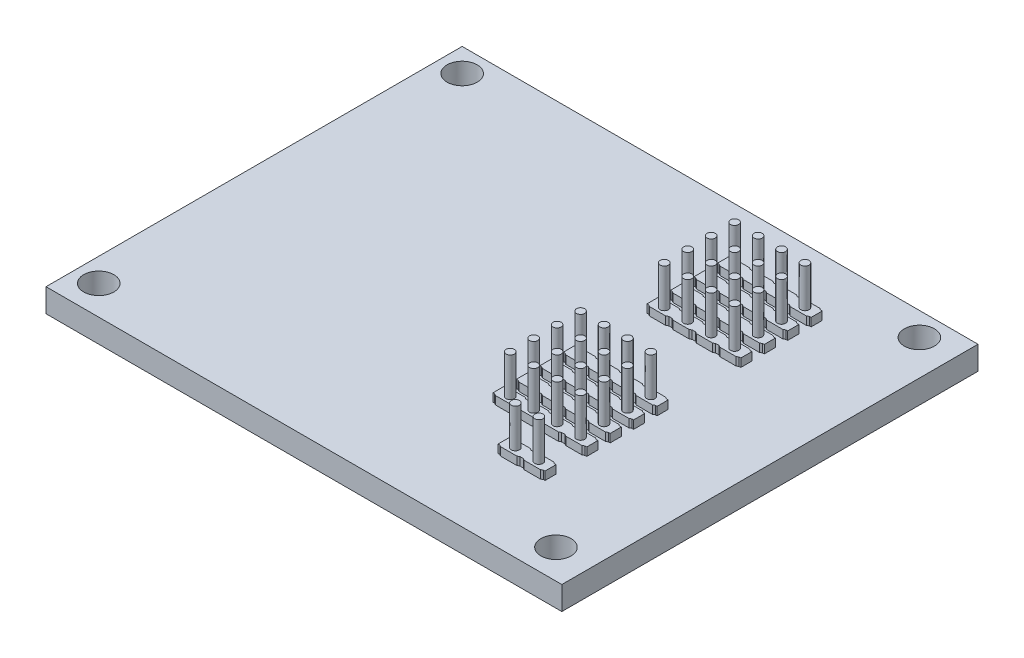
SolidWorks part; units mm, degrees
material "6061-T6 (SS)"
ref_plane "Front Plane" through (0, 0, 0) normal (0, 0, 1) x (1, 0, 0)
ref_plane "Top Plane" through (0, 0, 0) normal (0, 1, 0) x (1, 0, 0)
ref_plane "Right Plane" through (0, 0, 0) normal (1, 0, 0) x (0, 0, -1)
sketch "Sketch1" plane through (0, 0, 0) normal (0, 1, 0) x (1, 0, 0)
  line L1 (-27.94, -22.5425) -> (27.94, -22.5425)
  line L2 (-27.94, -22.5425) -> (-27.94, 22.5425)
  line L3 (-27.94, 22.5425) -> (27.94, 22.5425)
  line L4 (27.94, -22.5425) -> (27.94, 22.5425)
  line L5 (-27.94, -22.5425) -> (27.94, 22.5425) construction
  line L6 (-27.94, 22.5425) -> (27.94, -22.5425) construction
  point P0 (0, 0)
  dimension "D1" = 55.88
  dimension "D2" = 45.085
extrude "Boss-Extrude1" add sketch "Sketch1" along normal blind 2.54
hole_wizard "#4 Clearance Hole1" positions "Sketch2" profile "Sketch3" hole size "#4" standard "ANSI Inch" end condition up to next
sketch "Sketch2" plane through (0, 2.54, 0) normal (0, 1, 0) x (1, 0, 0)
  line L0 (27.94, 22.5425) -> (-27.94, 22.5425) construction
  line L1 (-27.94, 22.5425) -> (-27.94, -22.5425) construction
  point P0 (-25.4, -19.3675)
  point P2 (-25.4, 20.0025)
  point P4 (24.13, 20.0025)
  point P6 (24.13, -19.3675)
  dimension "D1" = 2.54
  dimension "D2" = 2.54
  dimension "D3" = 49.53
  dimension "D4" = 39.37
sketch "Sketch3" plane through (-25.4, 2.54, 19.3675) normal (1, 0, 0) x (0, 0, 1)
  line L0 (0, 0) -> (0, 2.54)
  line L1 (0, 2.54) -> (1.6319, 2.54)
  line L2 (1.6319, 2.54) -> (1.6319, 0)
  line L5 (1.6319, 0) -> (0, 0)
  line L11 (0, -6.35) -> (0, 107.95) construction
  dimension "Thru Hole Dia." = 3.2639
  dimension "Thru Hole Depth" = 2.54
sketch "Sketch4" plane through (0, 2.54, 0) normal (0, 1, 0) x (1, 0, 0)
  line L0 (27.94, 22.5425) -> (-27.94, 22.5425) construction
  line L1 (-27.94, 22.5425) -> (-27.94, -22.5425) construction
  circle A0 centre (16.002, 15.7353) radius 0.4445
  circle A1 centre (16.002, -0.9525) radius 0.4445
  dimension "D1" = 0.889
  dimension "D2" = 6.8072
  dimension "D3" = 43.942
  dimension "D4" = 23.495
extrude "Cut-Extrude1" cut sketch "Sketch4" against normal through all
pattern_linear "LPattern1" count 4 spacing 2.54 along (0, 0, 1) count 4 spacing 2.54 along (-1, 0, 0) of "Cut-Extrude1"
sketch "Sketch5" plane through (0, 2.54, 0) normal (0, 1, 0) x (1, 0, 0)
  circle A0 centre (16.002, -13.0845) radius 0.4445
  circle A1 centre (13.462, -13.0845) radius 0.4445
  circle A2 centre (16.002, -8.5725) radius 0.4445 construction
  point P6 (16.002, -8.5725)
  point P7 (13.462, -8.5725)
extrude "Cut-Extrude2" cut sketch "Sketch5" against normal through all
sketch "Sketch6" plane through (0, 2.54, 0) normal (0, 1, 0) x (1, 0, 0)
  line L0 (15.1229, 16.458) -> (14.918, 16.3342)
  line L1 (15.1229, 16.458) -> (16.8811, 16.458)
  line L2 (15.1229, 16.458) -> (15.1229, 15.0126)
  line L3 (15.1229, 15.0126) -> (16.8811, 15.0126)
  line L4 (16.8811, 16.458) -> (16.8811, 15.0126)
  line L5 (15.1229, 16.458) -> (16.8811, 15.0126) construction
  line L6 (15.1229, 15.0126) -> (16.8811, 16.458) construction
  line L7 (14.918, 16.3342) -> (14.732, 16.3342)
  line L8 (14.732, 16.3342) -> (14.732, 15.1364)
  line L9 (14.732, 15.1364) -> (14.918, 15.1364)
  line L10 (14.918, 15.1364) -> (15.1229, 15.0126)
  line L11 (16.002, 15.7353) -> (14.732, 15.7353) construction
  line L12 (16.002, 15.7353) -> (16.002, 15.0126) construction
  line L13 (16.8811, 16.458) -> (17.086, 16.3342)
  line L14 (16.002, 15.7353) -> (13.462, 15.7353) construction
  line L15 (14.732, 15.7353) -> (14.732, 15.1784) construction
  line L16 (17.086, 15.1364) -> (16.8811, 15.0126)
  line L17 (17.272, 15.7353) -> (17.272, 15.1784) construction
  line L18 (17.272, 15.1364) -> (17.086, 15.1364)
  line L19 (17.272, 16.3342) -> (17.272, 15.1364)
  line L20 (17.086, 16.3342) -> (17.272, 16.3342)
  point P0 (16.002, 15.7353)
  circle M18 centre (16.002, 15.7353) radius 0.4445
extrude "Boss-Extrude2" add sketch "Sketch6" along normal blind 0.889 contours L20 L13 L4 L16 L18 L19 | L4 L1 L2 L3 M18 | L9 L10 L2 L0 L7 L8
pattern_linear "LPattern3" count 4 spacing 2.54 along (0, 0, 1) count 4 spacing 2.54 along (-1, 0, 0) of "Boss-Extrude2"
pattern_linear "LPattern4" count 2 spacing 16.6878 along (0, 0, 1) of "Boss-Extrude2"
pattern_linear "LPattern5" count 4 spacing 2.54 along (0, 0, 1) count 4 spacing 2.54 along (-1, 0, 0) of "LPattern4"
pattern_linear "LPattern6" count 2 spacing 28.829 along (0, 0, 1) of "Boss-Extrude2"
pattern_linear "LPattern7" count 2 spacing 2.54 along (-1, 0, 0) of "LPattern6"
sketch "Sketch7" plane through (0, 2.54, 0) normal (0, 1, 0) x (1, 0, 0)
  circle A0 centre (16.002, 15.7353) radius 0.4445
  circle A1 centre (16.002, 15.7353) radius 0.4445 construction
  circle A2 centre (13.462, 15.7353) radius 0.4445
  circle A3 centre (10.922, 15.7353) radius 0.4445
  circle A4 centre (8.382, 15.7353) radius 0.4445
  circle A5 centre (8.382, 13.1953) radius 0.4445
  circle A6 centre (10.922, 13.1953) radius 0.4445
  circle A7 centre (13.462, 13.1953) radius 0.4445
  circle A8 centre (16.002, 13.1953) radius 0.4445
  circle A9 centre (16.002, 10.6553) radius 0.4445
  circle A10 centre (13.462, 10.6553) radius 0.4445
  circle A11 centre (10.922, 10.6553) radius 0.4445
  circle A12 centre (8.382, 10.6553) radius 0.4445
  circle A13 centre (8.382, 8.1153) radius 0.4445
  circle A14 centre (10.922, 8.1153) radius 0.4445
  circle A15 centre (13.462, 8.1153) radius 0.4445
  circle A16 centre (16.002, 8.1153) radius 0.4445
  circle A17 centre (16.002, -0.9525) radius 0.4445
  circle A18 centre (16.002, -3.4925) radius 0.4445
  circle A19 centre (16.002, -6.0325) radius 0.4445
  circle A20 centre (16.002, -8.5725) radius 0.4445
  circle A21 centre (13.462, -0.9525) radius 0.4445
  circle A22 centre (13.462, -3.4925) radius 0.4445
  circle A23 centre (13.462, -6.0325) radius 0.4445
  circle A24 centre (13.462, -8.5725) radius 0.4445
  circle A25 centre (10.922, -8.5725) radius 0.4445
  circle A26 centre (10.922, -6.0325) radius 0.4445
  circle A27 centre (10.922, -3.4925) radius 0.4445
  circle A28 centre (10.922, -0.9525) radius 0.4445
  circle A29 centre (8.382, -0.9525) radius 0.4445
  circle A30 centre (8.382, -3.4925) radius 0.4445
  circle A31 centre (8.382, -6.0325) radius 0.4445
  circle A32 centre (8.382, -8.5725) radius 0.4445
  circle A33 centre (16.002, -13.0937) radius 0.4445
  circle A34 centre (13.462, -13.0937) radius 0.4445
extrude "Boss-Extrude3" add sketch "Sketch7" along normal blind 5.08 and the other way blind 5.08
